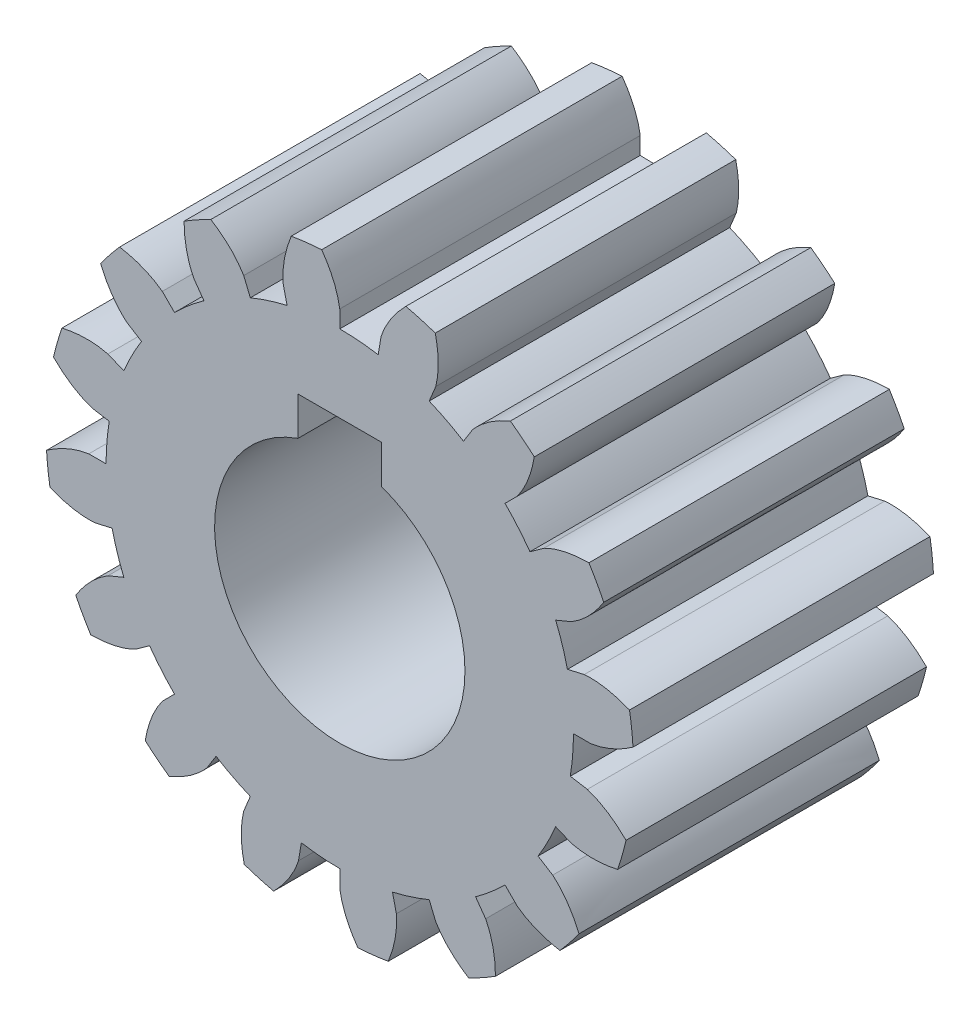
SolidWorks part; units mm, degrees
ref_plane "Front Plane" through (0, 0, 0) normal (0, 0, 1) x (1, 0, 0)
ref_plane "Top Plane" through (0, 0, 0) normal (0, 1, 0) x (1, 0, 0)
ref_plane "Right Plane" through (0, 0, 0) normal (1, 0, 0) x (0, 0, -1)
sketch "Sketch1" plane through (0, 0, 0) normal (0, 0, 1) x (1, 0, 0)
  line L0 (0, 0) -> (0, 15.035) construction
  line L1 (0, 0) -> (-3.2542, 14.6786) construction
  line L2 (0, 0) -> (-6.3541, 13.6263) construction
  line L3 (0, 0) -> (-9.1527, 11.9281) construction
  line L4 (0, 0) -> (-11.5175, 9.6643) construction
  line L5 (-3.2542, 14.6786) -> (-0.0519, 15.3885) construction
  line L6 (-6.3541, 13.6263) -> (-0.4087, 16.3987) construction
  line L7 (-9.1527, 11.9281) -> (-1.3461, 17.9183) construction
  line L8 (-11.5175, 9.6643) -> (-3.0841, 19.7148) construction
  line L9 (-0.2467, 15.9981) -> (-3.3679, 15.6415) construction
  line L10 (-1.8073, 15.8198) -> (0, 0) construction
  line L11 (-3.391, 14.6476) -> (-3.1576, 13.6393)
  line L12 (0, 15.035) -> (0, 14)
  circle A0 centre (0, 0) radius 15.035 construction
  circle A1 centre (0, 0) radius 16 construction
  arc A2 (-1.0838, 17.5666) -> (-2.9062, 17.3584) centre (0, 0) ccw
  circle A3 centre (0, 0) radius 14
  spline S0 degree 3 poles (0, 15.035) (-0.1423, 15.9662) (-0.5465, 16.8071) (-1.0838, 17.5666) knots 0 0 0 0 0.48587 0.48587 0.48587 0.48587
  spline S1 degree 3 poles (-3.391, 14.6476) (-3.4624, 15.587) (-3.2583, 16.4973) (-2.9062, 17.3584) knots 0 0 0 0 0.48587 0.48587 0.48587 0.48587
  point P11 (0, 0)
  dimension "D3" = 30.07
  dimension "D4" = 3.28
  dimension "D8" = 32
  dimension "D10" = 35.2
  dimension "D11" = 28
  dimension "D2" = 50
  dimension "D5" = 6.56
  dimension "D6" = 9.84
  dimension "D7" = 13.12
  dimension "D9" = 3.1416
  dimension "D1" = 5
sketch "Sketch2" plane through (0, 0, 0) normal (0, 0, 1) x (1, 0, 0)
  circle A0 centre (0, 0) radius 14
  dimension "D1" = 28
extrude "Boss-Extrude1" add sketch "Sketch2" along normal blind 18
sketch "Sketch3" plane through (0, 0, 18) normal (0, 0, 1) x (1, 0, 0)
  line L0 (-3.391, 14.6476) -> (-3.1576, 13.6393) construction
  line L1 (0, 15.035) -> (0, 14) construction
  line L2 (-3.391, 14.6476) -> (-3.1576, 13.6393)
  line L3 (0, 15.035) -> (0, 14)
  line L4 (5.7536, 13.8905) -> (5.3576, 12.9343)
  line L5 (2.4725, 14.8303) -> (2.3023, 13.8094)
  line L6 (10.6314, 10.6314) -> (9.8995, 9.8995)
  line L7 (7.9596, 12.7552) -> (7.4117, 11.8772)
  line L8 (13.8905, 5.7536) -> (12.9343, 5.3576)
  line L9 (12.2349, 8.7383) -> (11.3927, 8.1368)
  line L10 (15.035, 0) -> (14, 0)
  line L11 (14.6476, 3.391) -> (13.6393, 3.1576)
  line L12 (13.8905, -5.7536) -> (12.9343, -5.3576)
  line L13 (14.8303, -2.4725) -> (13.8094, -2.3023)
  line L14 (10.6314, -10.6314) -> (9.8995, -9.8995)
  line L15 (12.7552, -7.9596) -> (11.8772, -7.4117)
  line L16 (5.7536, -13.8905) -> (5.3576, -12.9343)
  line L17 (8.7383, -12.2349) -> (8.1368, -11.3927)
  line L18 (0, -15.035) -> (0, -14)
  line L19 (3.391, -14.6476) -> (3.1576, -13.6393)
  line L20 (-5.7536, -13.8905) -> (-5.3576, -12.9343)
  line L21 (-2.4725, -14.8303) -> (-2.3023, -13.8094)
  line L22 (-10.6314, -10.6314) -> (-9.8995, -9.8995)
  line L23 (-7.9596, -12.7552) -> (-7.4117, -11.8772)
  line L24 (-13.8905, -5.7536) -> (-12.9343, -5.3576)
  line L25 (-12.2349, -8.7383) -> (-11.3927, -8.1368)
  line L26 (-15.035, 0) -> (-14, 0)
  line L27 (-14.6476, -3.391) -> (-13.6393, -3.1576)
  line L28 (-13.8905, 5.7536) -> (-12.9343, 5.3576)
  line L29 (-14.8303, 2.4725) -> (-13.8094, 2.3023)
  line L30 (-10.6314, 10.6314) -> (-9.8995, 9.8995)
  line L31 (-12.7552, 7.9596) -> (-11.8772, 7.4117)
  line L32 (-5.7536, 13.8905) -> (-5.3576, 12.9343)
  line L33 (-8.7383, 12.2349) -> (-8.1368, 11.3927)
  circle A0 centre (0, 0) radius 14 construction
  arc A1 (-1.0838, 17.5666) -> (-2.9062, 17.3584) centre (0, 0) ccw construction
  arc A2 (0, 14) -> (-3.1576, 13.6393) centre (0, 0) ccw
  arc A3 (-1.0838, 17.5666) -> (-2.9062, 17.3584) centre (0, 0) ccw
  arc A4 (5.7212, 16.6442) -> (3.9578, 17.1492) centre (0, 0) ccw
  arc A5 (5.3576, 12.9343) -> (2.3023, 13.8094) centre (0, 0) ccw
  arc A6 (11.6551, 13.1878) -> (10.2193, 14.3292) centre (0, 0) ccw
  arc A7 (9.8995, 9.8995) -> (7.4117, 11.8772) centre (0, 0) ccw
  arc A8 (15.8147, 7.7237) -> (14.9249, 9.3277) centre (0, 0) ccw
  arc A9 (12.9343, 5.3576) -> (11.3927, 8.1368) centre (0, 0) ccw
  arc A10 (17.5666, 1.0838) -> (17.3584, 2.9062) centre (0, 0) ccw
  arc A11 (14, 0) -> (13.6393, 3.1576) centre (0, 0) ccw
  arc A12 (16.6442, -5.7212) -> (17.1492, -3.9578) centre (0, 0) ccw
  arc A13 (12.9343, -5.3576) -> (13.8094, -2.3023) centre (0, 0) ccw
  arc A14 (13.1878, -11.6551) -> (14.3292, -10.2193) centre (0, 0) ccw
  arc A15 (9.8995, -9.8995) -> (11.8772, -7.4117) centre (0, 0) ccw
  arc A16 (7.7237, -15.8147) -> (9.3277, -14.9249) centre (0, 0) ccw
  arc A17 (5.3576, -12.9343) -> (8.1368, -11.3927) centre (0, 0) ccw
  arc A18 (1.0838, -17.5666) -> (2.9062, -17.3584) centre (0, 0) ccw
  arc A19 (0, -14) -> (3.1576, -13.6393) centre (0, 0) ccw
  arc A20 (-5.7212, -16.6442) -> (-3.9578, -17.1492) centre (0, 0) ccw
  arc A21 (-5.3576, -12.9343) -> (-2.3023, -13.8094) centre (0, 0) ccw
  arc A22 (-11.6551, -13.1878) -> (-10.2193, -14.3292) centre (0, 0) ccw
  arc A23 (-9.8995, -9.8995) -> (-7.4117, -11.8772) centre (0, 0) ccw
  arc A24 (-15.8147, -7.7237) -> (-14.9249, -9.3277) centre (0, 0) ccw
  arc A25 (-12.9343, -5.3576) -> (-11.3927, -8.1368) centre (0, 0) ccw
  arc A26 (-17.5666, -1.0838) -> (-17.3584, -2.9062) centre (0, 0) ccw
  arc A27 (-14, 0) -> (-13.6393, -3.1576) centre (0, 0) ccw
  arc A28 (-16.6442, 5.7212) -> (-17.1492, 3.9578) centre (0, 0) ccw
  arc A29 (-12.9343, 5.3576) -> (-13.8094, 2.3023) centre (0, 0) ccw
  arc A30 (-13.1878, 11.6551) -> (-14.3292, 10.2193) centre (0, 0) ccw
  arc A31 (-9.8995, 9.8995) -> (-11.8772, 7.4117) centre (0, 0) ccw
  arc A32 (-7.7237, 15.8147) -> (-9.3277, 14.9249) centre (0, 0) ccw
  arc A33 (-5.3576, 12.9343) -> (-8.1368, 11.3927) centre (0, 0) ccw
  spline S0 degree 3 poles (-2966.6648, -420.2924) (3050.1275, 274.0042) (-3068.7799, -116.5932) (2997.3864, 106.274) knots -12.924957 -12.924957 -12.924957 -12.924957 14.95872 14.95872 14.95872 14.95872 only from (0, 15.035) to (-1.0838, 17.5666) construction
  spline S1 degree 3 poles (2985.0164, 259.638) (-3033.334, -420.9806) (3016.0026, 578.5418) (-2944.1207, -572.492) knots -12.924962 -12.924962 -12.924962 -12.924962 14.958725 14.958725 14.958725 14.958725 only from (-3.391, 14.6476) to (-2.9062, 17.3584) construction
  spline S2 degree 3 poles (0, 15.035) (-0.1423, 15.9662) (-0.5465, 16.8071) (-1.0838, 17.5666) knots 0 0 0 0 0.48587 0.48587 0.48587 0.48587
  spline S3 degree 3 poles (-3.391, 14.6476) (-3.4624, 15.587) (-3.2583, 16.4973) (-2.9062, 17.3584) knots 0 0 0 0 0.48587 0.48587 0.48587 0.48587
  spline S4 degree 3 poles (2.4725, 14.8303) (2.766, 15.7255) (3.303, 16.4884) (3.9578, 17.1492) knots 0 0 0 0 0.48587 0.48587 0.48587 0.48587
  spline S5 degree 3 poles (5.7536, 13.8905) (5.9785, 14.8054) (5.9269, 15.7369) (5.7212, 16.6442) knots 0 0 0 0 0.48587 0.48587 0.48587 0.48587
  spline S6 degree 3 poles (7.9596, 12.7552) (8.5734, 13.4699) (9.3614, 13.9693) (10.2193, 14.3292) knots 0 0 0 0 0.48587 0.48587 0.48587 0.48587
  spline S7 degree 3 poles (10.6314, 10.6314) (11.1892, 11.3905) (11.498, 12.2709) (11.6551, 13.1878) knots 0 0 0 0 0.48587 0.48587 0.48587 0.48587
  spline S8 degree 3 poles (12.2349, 8.7383) (13.0755, 9.1637) (13.9946, 9.3235) (14.9249, 9.3277) knots 0 0 0 0 0.48587 0.48587 0.48587 0.48587
  spline S9 degree 3 poles (13.8905, 5.7536) (14.6964, 6.2415) (15.3186, 6.9367) (15.8147, 7.7237) knots 0 0 0 0 0.48587 0.48587 0.48587 0.48587
  spline S10 degree 3 poles (14.6476, 3.391) (15.587, 3.4624) (16.4973, 3.2583) (17.3584, 2.9062) knots 0 0 0 0 0.48587 0.48587 0.48587 0.48587
  spline S11 degree 3 poles (15.035, 0) (15.9662, 0.1423) (16.8071, 0.5465) (17.5666, 1.0838) knots 0 0 0 0 0.48587 0.48587 0.48587 0.48587
  spline S12 degree 3 poles (14.8303, -2.4725) (15.7255, -2.766) (16.4884, -3.303) (17.1492, -3.9578) knots 0 0 0 0 0.48587 0.48587 0.48587 0.48587
  spline S13 degree 3 poles (13.8905, -5.7536) (14.8054, -5.9785) (15.7369, -5.9269) (16.6442, -5.7212) knots 0 0 0 0 0.48587 0.48587 0.48587 0.48587
  spline S14 degree 3 poles (12.7552, -7.9596) (13.4699, -8.5734) (13.9693, -9.3614) (14.3292, -10.2193) knots 0 0 0 0 0.48587 0.48587 0.48587 0.48587
  spline S15 degree 3 poles (10.6314, -10.6314) (11.3905, -11.1892) (12.2709, -11.498) (13.1878, -11.6551) knots 0 0 0 0 0.48587 0.48587 0.48587 0.48587
  spline S16 degree 3 poles (8.7383, -12.2349) (9.1637, -13.0755) (9.3235, -13.9946) (9.3277, -14.9249) knots 0 0 0 0 0.48587 0.48587 0.48587 0.48587
  spline S17 degree 3 poles (5.7536, -13.8905) (6.2415, -14.6964) (6.9367, -15.3186) (7.7237, -15.8147) knots 0 0 0 0 0.48587 0.48587 0.48587 0.48587
  spline S18 degree 3 poles (3.391, -14.6476) (3.4624, -15.587) (3.2583, -16.4973) (2.9062, -17.3584) knots 0 0 0 0 0.48587 0.48587 0.48587 0.48587
  spline S19 degree 3 poles (0, -15.035) (0.1423, -15.9662) (0.5465, -16.8071) (1.0838, -17.5666) knots 0 0 0 0 0.48587 0.48587 0.48587 0.48587
  spline S20 degree 3 poles (-2.4725, -14.8303) (-2.766, -15.7255) (-3.303, -16.4884) (-3.9578, -17.1492) knots 0 0 0 0 0.48587 0.48587 0.48587 0.48587
  spline S21 degree 3 poles (-5.7536, -13.8905) (-5.9785, -14.8054) (-5.9269, -15.7369) (-5.7212, -16.6442) knots 0 0 0 0 0.48587 0.48587 0.48587 0.48587
  spline S22 degree 3 poles (-7.9596, -12.7552) (-8.5734, -13.4699) (-9.3614, -13.9693) (-10.2193, -14.3292) knots 0 0 0 0 0.48587 0.48587 0.48587 0.48587
  spline S23 degree 3 poles (-10.6314, -10.6314) (-11.1892, -11.3905) (-11.498, -12.2709) (-11.6551, -13.1878) knots 0 0 0 0 0.48587 0.48587 0.48587 0.48587
  spline S24 degree 3 poles (-12.2349, -8.7383) (-13.0755, -9.1637) (-13.9946, -9.3235) (-14.9249, -9.3277) knots 0 0 0 0 0.48587 0.48587 0.48587 0.48587
  spline S25 degree 3 poles (-13.8905, -5.7536) (-14.6964, -6.2415) (-15.3186, -6.9367) (-15.8147, -7.7237) knots 0 0 0 0 0.48587 0.48587 0.48587 0.48587
  spline S26 degree 3 poles (-14.6476, -3.391) (-15.587, -3.4624) (-16.4973, -3.2583) (-17.3584, -2.9062) knots 0 0 0 0 0.48587 0.48587 0.48587 0.48587
  spline S27 degree 3 poles (-15.035, 0) (-15.9662, -0.1423) (-16.8071, -0.5465) (-17.5666, -1.0838) knots 0 0 0 0 0.48587 0.48587 0.48587 0.48587
  spline S28 degree 3 poles (-14.8303, 2.4725) (-15.7255, 2.766) (-16.4884, 3.303) (-17.1492, 3.9578) knots 0 0 0 0 0.48587 0.48587 0.48587 0.48587
  spline S29 degree 3 poles (-13.8905, 5.7536) (-14.8054, 5.9785) (-15.7369, 5.9269) (-16.6442, 5.7212) knots 0 0 0 0 0.48587 0.48587 0.48587 0.48587
  spline S30 degree 3 poles (-12.7552, 7.9596) (-13.4699, 8.5734) (-13.9693, 9.3614) (-14.3292, 10.2193) knots 0 0 0 0 0.48587 0.48587 0.48587 0.48587
  spline S31 degree 3 poles (-10.6314, 10.6314) (-11.3905, 11.1892) (-12.2709, 11.498) (-13.1878, 11.6551) knots 0 0 0 0 0.48587 0.48587 0.48587 0.48587
  spline S32 degree 3 poles (-8.7383, 12.2349) (-9.1637, 13.0755) (-9.3235, 13.9946) (-9.3277, 14.9249) knots 0 0 0 0 0.48587 0.48587 0.48587 0.48587
  spline S33 degree 3 poles (-5.7536, 13.8905) (-6.2415, 14.6964) (-6.9367, 15.3186) (-7.7237, 15.8147) knots 0 0 0 0 0.48587 0.48587 0.48587 0.48587
  point P101 (0, 0)
  dimension "D1" = 16
extrude "Boss-Extrude2" add sketch "Sketch3" against normal through all
sketch "Sketch4" plane through (0, 0, 18) normal (0, 0, 1) x (1, 0, 0)
  circle A0 centre (0, 0) radius 7.5
  dimension "D1" = 15
extrude "Cut-Extrude1" cut sketch "Sketch4" against normal through all
sketch "Sketch5" plane through (0, 0, 18) normal (0, 0, 1) x (1, 0, 0)
  line L0 (0, 0) -> (0, 7.5) construction
  line L1 (-2.5, 7.0711) -> (2.5, 7.0711)
  line L2 (-2.5, 7.0711) -> (-2.5, 9.3711)
  line L3 (-2.5, 9.3711) -> (2.5, 9.3711)
  line L4 (2.5, 7.0711) -> (2.5, 9.3711)
  circle A0 centre (0, 0) radius 7.5 construction
  dimension "D1" = 2.3
  dimension "D2" = 5
extrude "Cut-Extrude2" cut sketch "Sketch5" against normal blind 6
